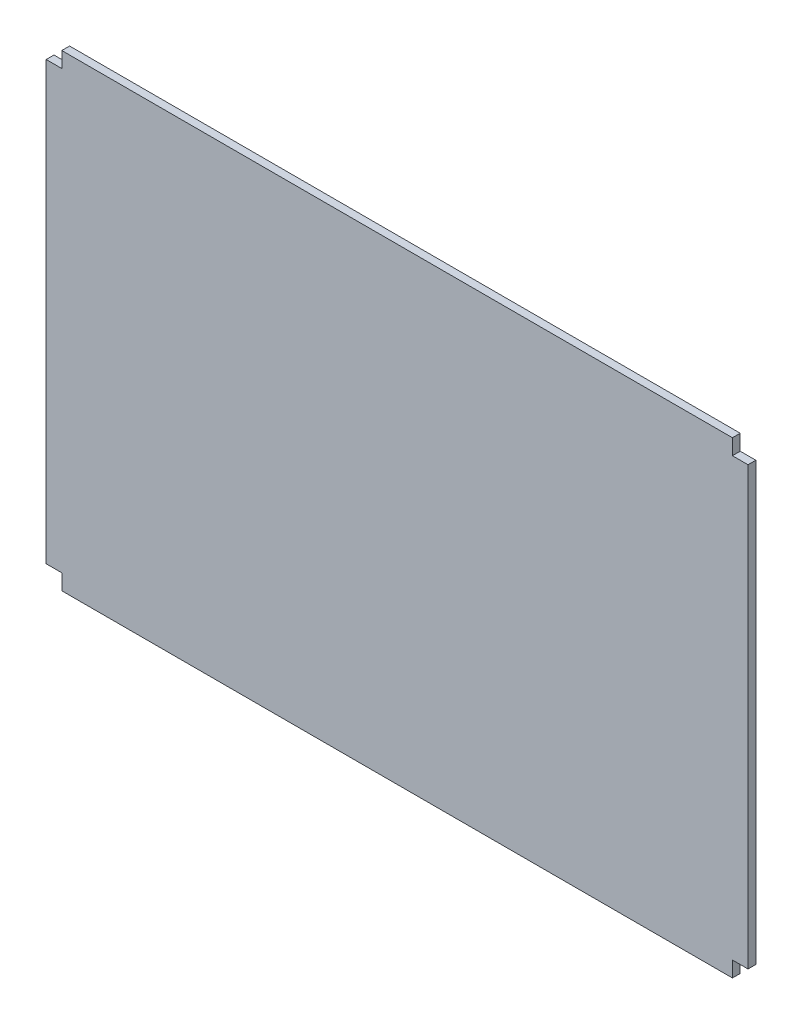
SolidWorks part; units mm, degrees
ref_plane "Front Plane" through (0, 0, 0) normal (0, 0, 1) x (1, 0, 0)
ref_plane "Top Plane" through (0, 0, 0) normal (0, 1, 0) x (1, 0, 0)
ref_plane "Right Plane" through (0, 0, 0) normal (1, 0, 0) x (0, 0, -1)
sketch "Sketch2" plane through (0, 0, 0) normal (0, 0, 1) x (1, 0, 0)
  line L1 (0, 0) -> (900, 0)
  line L2 (0, 0) -> (0, 600)
  line L3 (0, 600) -> (900, 600)
  line L4 (900, 0) -> (900, 600)
  dimension "D1" = 900
  dimension "D2" = 600
extrude "Boss-Extrude1" add sketch "Sketch2" along normal blind 10
sketch "Sketch3" plane through (0, 0, 10) normal (0, 0, 1) x (1, 0, 0)
  line L1 (0, 600) -> (20, 600)
  line L2 (0, 600) -> (0, 580)
  line L3 (0, 580) -> (20, 580)
  line L4 (20, 600) -> (20, 580)
  line L5 (900, 600) -> (880, 600)
  line L6 (900, 600) -> (900, 580)
  line L7 (900, 580) -> (880, 580)
  line L8 (880, 600) -> (880, 580)
  line L9 (900, 0) -> (880, 0)
  line L10 (900, 0) -> (900, 20)
  line L11 (900, 20) -> (880, 20)
  line L12 (880, 0) -> (880, 20)
  line L13 (0, 0) -> (20, 0)
  line L14 (0, 0) -> (0, 20)
  line L15 (0, 20) -> (20, 20)
  line L16 (20, 0) -> (20, 20)
  dimension "D1" = 20
extrude "Cut-Extrude1" cut sketch "Sketch3" against normal through all
